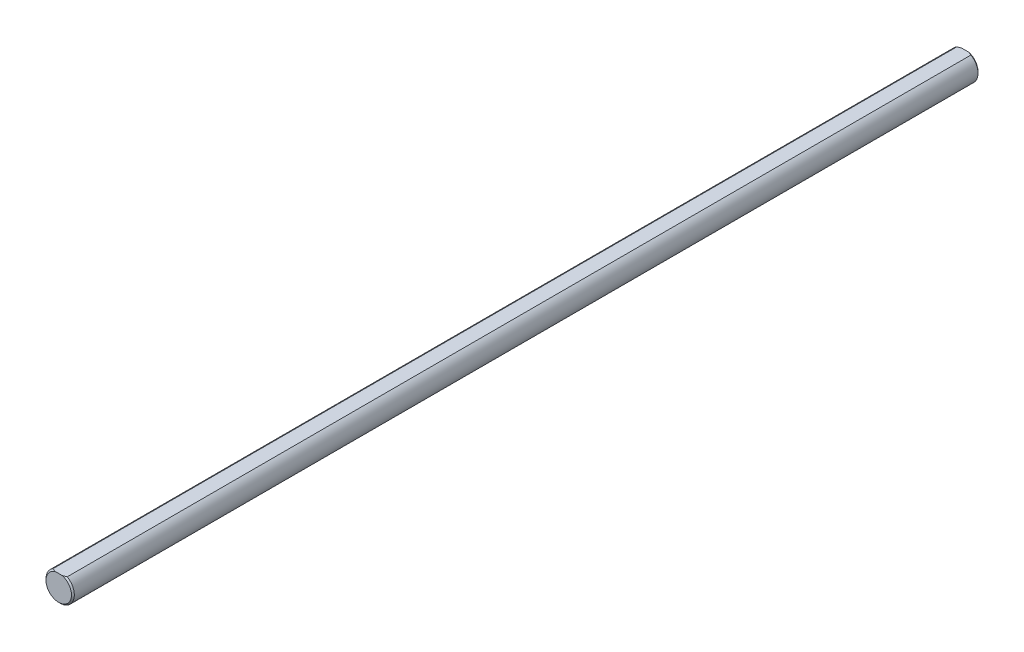
SolidWorks part; units mm, degrees
ref_plane "Front Plane" through (0, 0, 0) normal (0, 0, 1) x (1, 0, 0)
ref_plane "Top Plane" through (0, 0, 0) normal (0, 1, 0) x (1, 0, 0)
ref_plane "Right Plane" through (0, 0, 0) normal (1, 0, 0) x (0, 0, -1)
sketch "Sketch1" plane through (0, 0, 0) normal (0, 0, 1) x (1, 0, 0)
  circle A1 centre (0, 0) radius 4.7625 construction
  dimension "Diameter" = 9.525
sketch "Sketch2" plane through (0, 0, 0) normal (1, 0, 0) x (0, 0, -1)
  line L0 (-152.4, 4.7625) -> (152.4, 4.7625) construction
  line L1 (0, 4.7625) -> (0, -4.7625) construction
  line L2 (0, 4.7625) -> (0, -4.7625) construction
  point P2 (0, 4.7625)
  point P3 (133.35, 4.7625)
  point P4 (-133.35, 4.7625)
  dimension "Length" = 304.8
  dimension "D2" = 19.05
  dimension "D1" = 19.05
sketch "Sketch3" plane through (0, 0, 0) normal (0, 0, 1) x (1, 0, 0)
  circle A1 centre (0, 0) radius 4.7625 construction
  circle A3 centre (0, 0) radius 4.7625
extrude "Boss-Extrude2" add sketch "Sketch3" along normal up to vertex (152.4 mm away) and the other way up to vertex (152.4 mm away) up to point (0, 4.7625, 152.4) other way up to point (0, 4.7625, -152.4)
sketch "Sketch10" plane through (0, 0, 0) normal (0, 0, 1) x (1, 0, 0)
  line L0 (-2.3813, 4.1244) -> (2.3813, 4.1244)
  line L1 (0, 0) -> (0, 4.7625) construction
  circle A0 centre (0, 0) radius 4.7625 construction
  circle A1 centre (0, 0) radius 4.7625 construction
  arc A2 (-2.3813, 4.1244) -> (2.3813, 4.1244) centre (0, 0) cw
  dimension "D1" = 0.6381
  dimension "D2" = 4.7625
extrude "Cut-Extrude5" cut sketch "Sketch10" against normal through all both and the other way through all
chamfer "Chamfer1" distance 0.4762 angle 45 4 edges at (0, -4.7625, 152.4) (0, -4.7625, -152.4) (0, 4.1244, -152.4) (0, 4.1244, 152.4)
equation "\"D1@Chamfer1\"= \"Diameter@Sketch1\" / 20"
equation "\"D1@Sketch2\"=\"Diameter@Sketch1\"*2"
equation "\"D2@Sketch2\"=\"D1@Sketch2\""
